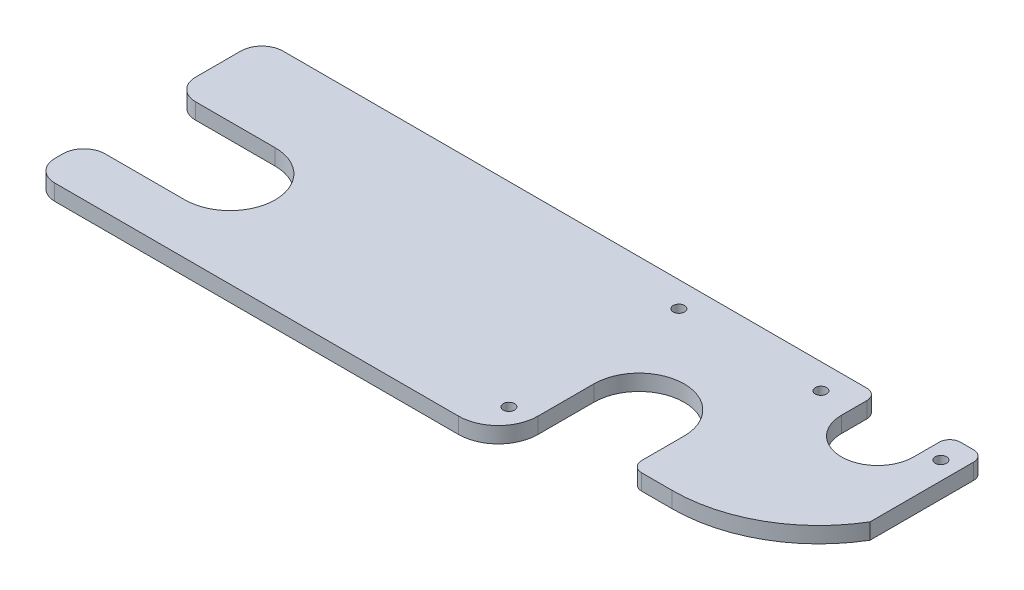
SolidWorks part; units mm, degrees
material "PC High Viscosity"
ref_plane "Front Plane" through (0, 0, 0) normal (0, 0, 1) x (1, 0, 0)
ref_plane "Top Plane" through (0, 0, 0) normal (0, 1, 0) x (1, 0, 0)
ref_plane "Right Plane" through (0, 0, 0) normal (1, 0, 0) x (0, 0, -1)
sketch "Sketch1" plane through (0, 0, 0) normal (0, 1, 0) x (1, 0, 0)
  line L1 (25.4, 0) -> (277.8125, 0)
  line L3 (12.7, 136.525) -> (23.8125, 136.525)
  line L4 (431.8, 0) -> (431.8, 136.525) construction
  line L6 (182.5625, 0) -> (182.5625, 117.943) construction
  line L7 (277.8125, 57.15) -> (277.8125, 0)
  line L8 (331.7875, 57.15) -> (331.7875, 0)
  line L9 (368.046, 114.935) -> (368.046, 136.525)
  line L10 (411.226, 114.935) -> (411.226, 136.525)
  line L11 (411.226, 136.525) -> (431.8, 136.525)
  line L12 (331.7875, 0) -> (431.8, 0) construction
  line L13 (23.8125, 136.525) -> (368.046, 136.525)
  line L14 (331.7875, 0) -> (357.1875, 0)
  line L15 (431.8, 136.525) -> (431.8, 68.2625)
  line L16 (60.325, 30.1625) -> (22.225, 30.1625)
  line L17 (0, 17.4625) -> (0, 12.7)
  line L18 (12.7, 0) -> (25.4, 0)
  line L19 (60.325, 84.1375) -> (22.225, 84.1375)
  line L20 (0, 96.8375) -> (0, 123.825)
  line L21 (22.225, 84.1375) -> (0, 84.1375)
  line L22 (0, 84.1375) -> (0, 96.8375)
  line L23 (22.225, 30.1625) -> (0, 30.1625)
  line L24 (0, 30.1625) -> (0, 17.4625)
  arc A0 (60.325, 30.1625) -> (87.3125, 57.15) centre (60.325, 57.15) ccw
  arc A1 (277.8125, 57.15) -> (331.7875, 57.15) centre (304.8, 57.15) cw
  arc A2 (368.046, 114.935) -> (411.226, 114.935) centre (389.636, 114.935) ccw
  arc A3 (357.1875, 0) -> (431.8, 68.2625) centre (357.1875, 74.9078) ccw
  arc A5 (60.325, 84.1375) -> (87.3125, 57.15) centre (60.325, 57.15) cw
  arc A6 (0, 12.7) -> (12.7, 0) centre (12.7, 12.7) ccw
  arc A8 (0, 123.825) -> (12.7, 136.525) centre (12.7, 123.825) cw
  point P27 (0, 0)
  point P35 (0, 0)
  point P40 (0, 136.525)
  dimension "D3" = 53.975
  dimension "D4" = 12.7
  dimension "D5" = 57.15
  dimension "D8" = 43.18
  dimension "D12" = 21.59
  dimension "D14" = 12.7
  dimension "D15" = 74.9078
  dimension "D1" = 431.8
  dimension "D2" = 136.525
  dimension "D6" = 122.2375
  dimension "D7" = 244.475
  dimension "D9" = 42.164
  dimension "D10" = 127
  dimension "D11" = 25.4
  dimension "D13" = 136.525
  dimension "D16" = 57.15
  dimension "D17" = 57.15
extrude "Boss-Extrude2" add sketch "Sketch1" along normal blind 9.525 contours L13 L9 A2 L10 L11 L15 A3 L14 L8 A1 L7 L1 L18 A6 L17 L24 L23 L16 A0 A5 L19 L21 L22 L20 A8 L3
sketch "Sketch2" plane through (0, 9.525, 0) normal (0, 1, 0) x (1, 0, 0)
  line L0 (331.7875, 0) -> (331.7875, 25.4)
  line L5 (431.8, 136.525) -> (431.8, 68.2625) construction
  line L21 (331.7875, 25.4) -> (356.3938, 25.4)
  line L22 (331.7875, 57.15) -> (331.7875, 0) construction
  line L23 (331.7875, 0) -> (357.1875, 0) construction
  line L25 (331.7875, 0) -> (357.1875, 0)
  arc A2 (356.3938, 25.4) -> (431.8, 68.2625) centre (356.3938, 113.1608) ccw
  arc A3 (357.1875, 0) -> (431.8, 68.2625) centre (357.1875, 74.9078) ccw
  dimension "D3" = 25.4
extrude "Cut-Extrude2" cut sketch "Sketch2" against normal through all
hole_wizard "1/4 Clearance Hole1" positions "Sketch3" profile "Sketch4" hole size "1/4" standard "ANSI Inch" end condition through all
sketch "Sketch3" plane through (0, 9.525, 0) normal (0, 1, 0) x (1, 0, 0)
  line L1 (12.7, 136.525) -> (368.046, 136.525) construction
  line L6 (304.8, 84.1375) -> (304.8, 136.525) construction
  line L10 (431.8, 136.525) -> (431.8, 68.2625) construction
  line L11 (12.7, 136.525) -> (368.046, 136.525) construction
  line L13 (368.046, 114.935) -> (368.046, 136.525) construction
  line L14 (12.7, 0) -> (277.8125, 0) construction
  line L15 (277.8125, 57.15) -> (277.8125, 0) construction
  arc A0 (331.7875, 57.15) -> (277.8125, 57.15) centre (304.8, 57.15) ccw construction
  point P0 (420.9542, 121.4438)
  point P2 (349.269, 121.4438)
  point P4 (264.3188, 121.4438)
  point P6 (264.3188, 19.8438)
  dimension "D1" = 10.8458
  dimension "D2" = 15.0812
  dimension "D3" = 40.4812
  dimension "D4" = 18.777
  dimension "D5" = 19.8438
  dimension "D6" = 13.4938
sketch "Sketch4" plane through (420.9542, 9.525, -121.4438) normal (1, 0, 0) x (0, 0, 1)
  line L0 (0, 0) -> (0, 9.525)
  line L1 (0, 9.525) -> (3.3782, 9.525)
  line L2 (3.3782, 9.525) -> (3.3782, 0)
  line L5 (3.3782, 0) -> (0, 0)
  line L11 (0, -6.35) -> (0, 107.95) construction
  dimension "Thru Hole Dia." = 6.7564
  dimension "Thru Hole Depth" = 9.525
fillet "Fillet5" radius 23.8125 1 edges at (277.8125, 4.7625, 0)
fillet "Fillet6" radius 12.7 2 edges at (0, 4.7625, -30.1625) (0, 4.7625, -84.1375)
fillet "Fillet7" radius 6.35 4 edges at (368.046, 4.7625, -136.525) (431.8, 4.7625, -136.525) (411.226, 4.7625, -136.525) (331.7875, 4.7625, -25.4)
